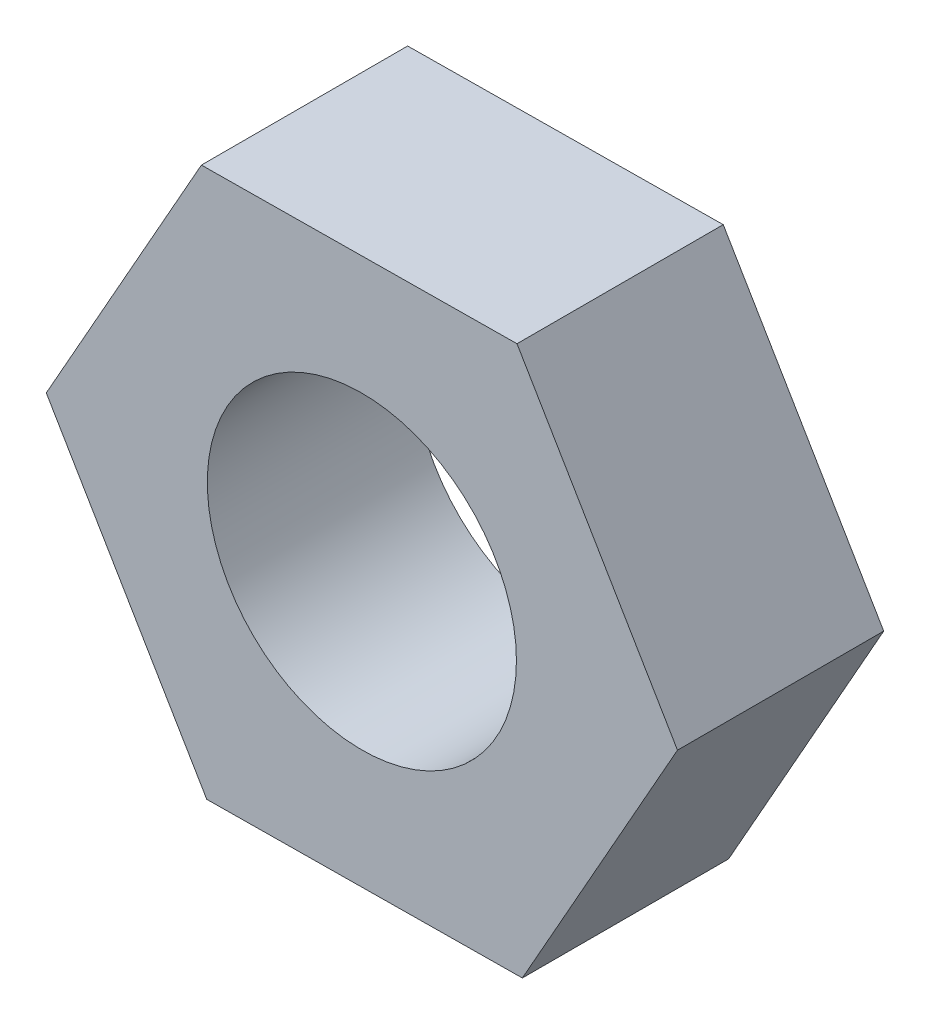
SolidWorks part; units mm, degrees
material "Stop odlewniczy stali"
ref_plane "Front" through (0, 0, 0) normal (0, 0, 1) x (1, 0, 0)
ref_plane "Top" through (0, 0, 0) normal (0, 1, 0) x (1, 0, 0)
ref_plane "Right" through (0, 0, 0) normal (1, 0, 0) x (0, 0, -1)
sketch "Szkic1" plane through (0, 0, 0) normal (0, 0, 1) x (1, 0, 0)
  line L1 (-3.2291, 5.4687) -> (-6.3505, -0.0621)
  line L2 (-6.3505, -0.0621) -> (-3.1215, -5.5308)
  line L3 (-3.1215, -5.5308) -> (3.2291, -5.4687)
  line L4 (3.2291, -5.4687) -> (6.3505, 0.0621)
  line L5 (6.3505, 0.0621) -> (3.1215, 5.5308)
  line L6 (3.1215, 5.5308) -> (-3.2291, 5.4687)
  circle A0 centre (0, 0) radius 5.5 construction
  dimension "D1" = 11
extrude "Dodanie-wyciągnięcie1" add sketch "Szkic1" along normal blind 4.15
sketch "Szkic2" plane through (0, 0, 4.15) normal (0, 0, 1) x (1, 0, 0)
  circle A0 centre (0, 0) radius 3.11
extrude "Wytnij-wyciągnięcie1" cut sketch "Szkic2" against normal through all contours A0
